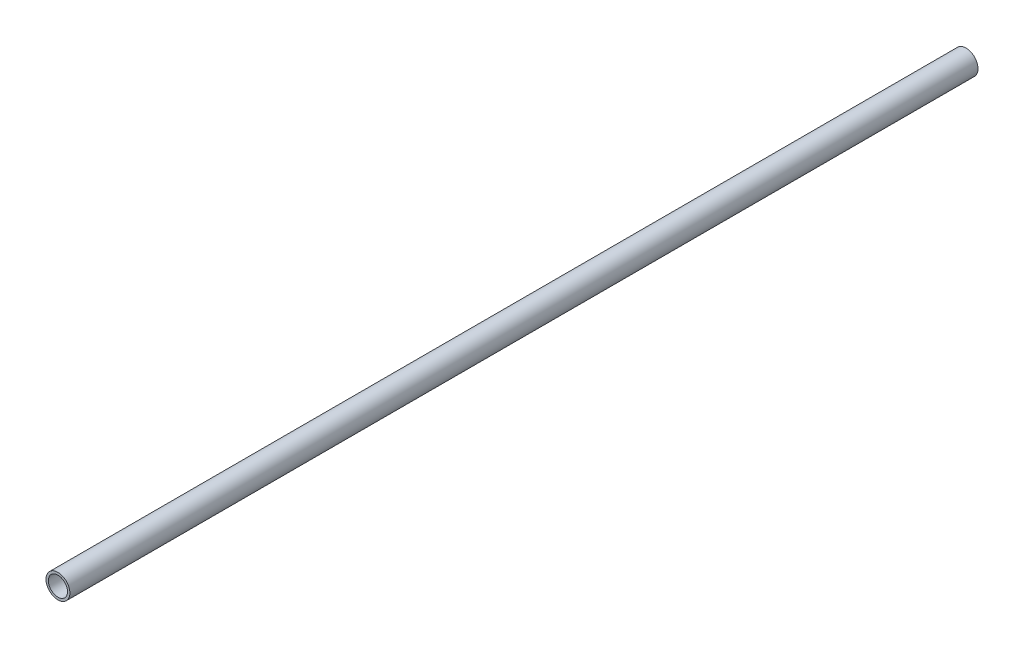
SolidWorks part; units mm, degrees
ref_plane "Plano frontal" through (0, 0, 0) normal (0, 0, 1) x (1, 0, 0)
ref_plane "Plano superior" through (0, 0, 0) normal (0, 1, 0) x (1, 0, 0)
ref_plane "Plano direito" through (0, 0, 0) normal (1, 0, 0) x (0, 0, -1)
sketch "Esboço1" plane through (0, 0, 0) normal (0, 0, 1) x (1, 0, 0)
  circle A0 centre (0, 0) radius 5
  circle A1 centre (0, 0) radius 4
  dimension "D1" = 10
  dimension "D2" = 8
extrude "Ressalto-extrusão1" add sketch "Esboço1" along normal blind 380
